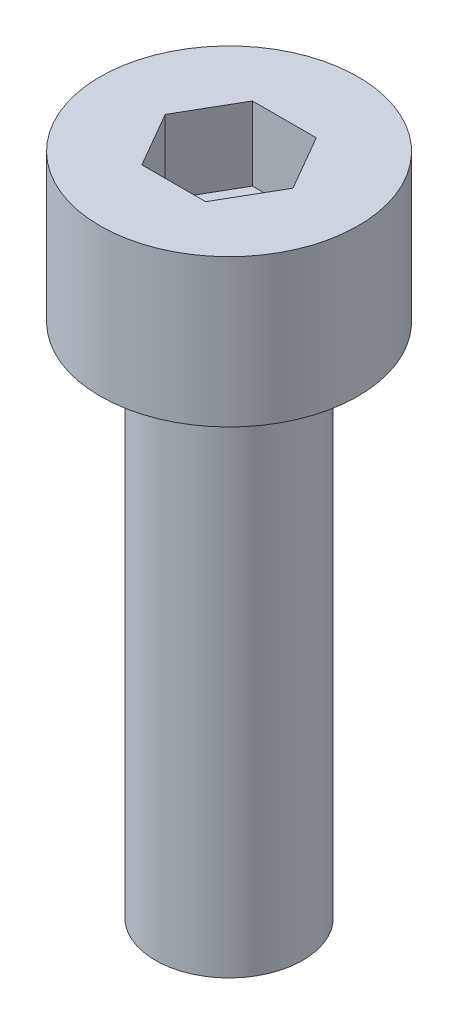
SolidWorks part; units mm, degrees
material "AISI 304"
ref_plane "前视基准面" through (0, 0, 0) normal (0, 0, 1) x (1, 0, 0)
ref_plane "上视基准面" through (0, 0, 0) normal (0, 1, 0) x (1, 0, 0)
ref_plane "右视基准面" through (0, 0, 0) normal (1, 0, 0) x (0, 0, -1)
sketch "草图1" plane through (0, 0, 0) normal (0, 1, 0) x (1, 0, 0)
  circle A0 centre (0, 0) radius 3.5
  dimension "D1" = 7
extrude "杯头" add sketch "草图1" along normal blind 4
sketch "草图2" plane through (0, 4, 0) normal (0, 1, 0) x (1, 0, 0)
  line L1 (1.7321, 0) -> (0.866, 1.5)
  line L2 (0.866, 1.5) -> (-0.866, 1.5)
  line L3 (-0.866, 1.5) -> (-1.7321, 0)
  line L4 (-1.7321, 0) -> (-0.866, -1.5)
  line L5 (-0.866, -1.5) -> (0.866, -1.5)
  line L6 (0.866, -1.5) -> (1.7321, 0)
  circle A0 centre (0, 0) radius 1.5 construction
  dimension "D1" = 3
extrude "内六角口" cut sketch "草图2" against normal blind 2
sketch "草图3" plane through (0, 0, 0) normal (0, -1, 0) x (1, 0, 0)
  circle A0 centre (0, 0) radius 2
  dimension "D1" = 4
extrude "螺纹长度" add sketch "草图3" along normal blind 14
sketch "草图8" [suppressed] plane through (0, 0, 0) normal (0, 0, 1) x (1, 0, 0)
  line L0 (-1.3, -14) -> (-2, -13.3)
  line L1 (-2, -14) -> (2, -14) construction
  line L2 (-2, 0) -> (-2, -14) construction
  line L3 (-2, -13.3) -> (-2, -14)
  line L4 (-2, -14) -> (-1.3, -14)
  dimension "D1" = 0.7
  dimension "D2" = 0.7
